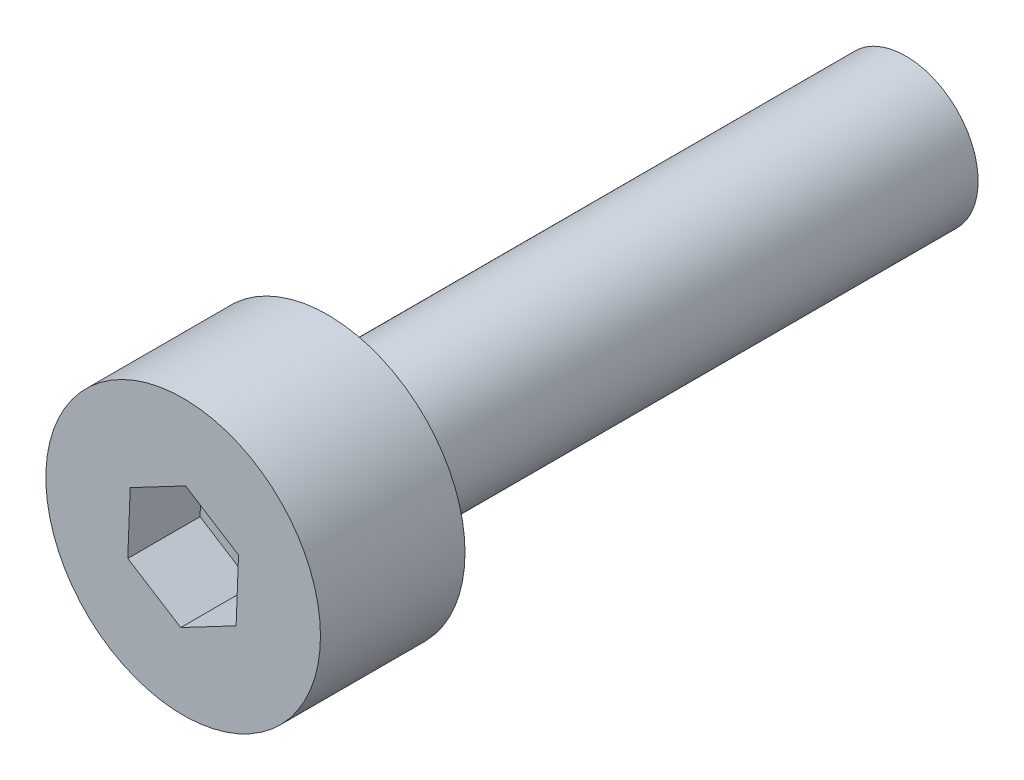
SolidWorks part; units mm, degrees
ref_plane "前视基准面" through (0, 0, 0) normal (0, 0, 1) x (1, 0, 0)
ref_plane "上视基准面" through (0, 0, 0) normal (0, 1, 0) x (1, 0, 0)
ref_plane "右视基准面" through (0, 0, 0) normal (1, 0, 0) x (0, 0, -1)
sketch "草图1" plane through (0, 0, 0) normal (0, 0, 1) x (1, 0, 0)
  circle A0 centre (0, 0) radius 1.9
  dimension "D1" = 3.8
extrude "凸台-拉伸1" add sketch "草图1" along normal blind 2
sketch "草图2" plane through (0, 0, 0) normal (0, 0, -1) x (-1, 0, 0)
  circle A0 centre (0, 0) radius 1
  circle A1 centre (0, 0) radius 1.9
  circle A2 centre (0, 0) radius 1.9
  dimension "D2" = 2
  dimension "D1" = 0
extrude "凸台-拉伸2" add sketch "草图2" along normal blind 8 contours A0
sketch "草图3" plane through (0, 0, 2) normal (0, 0, 1) x (1, 0, 0)
  line L1 (0.7326, -0.4618) -> (0.7662, 0.4036)
  line L2 (0.7662, 0.4036) -> (0.0336, 0.8654)
  line L3 (0.0336, 0.8654) -> (-0.7326, 0.4618)
  line L4 (-0.7326, 0.4618) -> (-0.7662, -0.4036)
  line L5 (-0.7662, -0.4036) -> (-0.0336, -0.8654)
  line L6 (-0.0336, -0.8654) -> (0.7326, -0.4618)
  circle A0 centre (0, 0) radius 0.75 construction
  circle A1 centre (0, 0) radius 1.9
  circle A2 centre (0, 0) radius 1.9
  dimension "D2" = 1.5
  dimension "D1" = 0
extrude "切除-拉伸1" cut sketch "草图3" against normal blind 1 contours L5 L6 L1 L2 L3 L4
